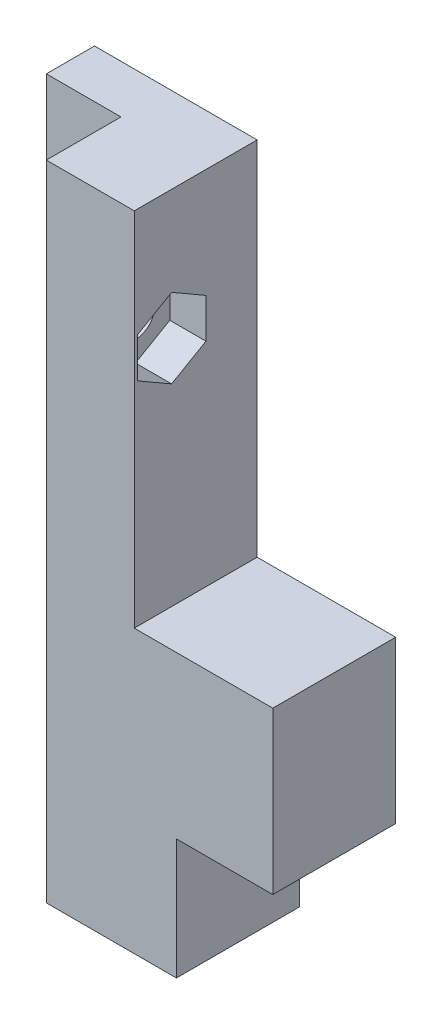
SolidWorks part; units mm, degrees
ref_plane "Alzado" through (0, 0, 0) normal (0, 0, 1) x (1, 0, 0)
ref_plane "Planta" through (0, 0, 0) normal (0, 1, 0) x (1, 0, 0)
ref_plane "Vista lateral" through (0, 0, 0) normal (1, 0, 0) x (0, 0, -1)
sketch "Croquis1" plane through (0, 0, 0) normal (0, 0, 1) x (1, 0, 0)
  line L1 (0, 0) -> (25, 0)
  line L2 (0, 0) -> (0, 35)
  line L3 (0, 35) -> (13.5, 35)
  line L4 (25, 0) -> (25, 5)
  line L7 (25, 5) -> (13.5, 5)
  line L8 (13.5, 35) -> (13.5, 5)
  dimension "D1" = 25
  dimension "D2" = 35
  dimension "D3" = 13.5
  dimension "D4" = 5
extrude "Saliente-Extruir1" add sketch "Croquis1" along normal blind 4
sketch "Croquis2" plane through (0, 0, 4) normal (0, 0, 1) x (1, 0, 0)
  line L0 (6.2, 35) -> (6.2, 0)
  line L1 (0, 35) -> (0, 0) construction
  line L6 (0, 35) -> (0, 0)
  line L7 (0, 0) -> (25, 0)
  line L8 (25, 0) -> (25, 5)
  line L9 (25, 5) -> (13.5, 5)
  line L10 (13.5, 5) -> (13.5, 35)
  line L11 (13.5, 35) -> (0, 35)
  line L13 (6.2, 0) -> (25, 0)
  line L14 (25, 0) -> (25, 5)
  line L15 (25, 5) -> (13.5, 5)
  line L16 (13.5, 5) -> (13.5, 35)
  line L17 (13.5, 35) -> (6.2, 35)
  dimension "D2" = 6.2
  dimension "D1" = 0
extrude "Saliente-Extruir2" add sketch "Croquis2" along normal blind 6.2
sketch "Croquis3" plane through (6.2, 0, 0) normal (-1, 0, 0) x (0, 0, 1)
  line L0 (7.1, 35) -> (7.1, 24.3) construction
  line L1 (10.2, 35) -> (4, 35) construction
  circle A0 centre (7.1, 24.3) radius 1.6
  dimension "D2" = 3.2
  dimension "D1" = 10.7
extrude "Cortar-Extruir1" cut sketch "Croquis3" against normal up to next
sketch "Croquis4" plane through (13.5, 0, 0) normal (1, 0, 0) x (0, 0, -1)
  line L1 (-7.1, 27.5909) -> (-9.95, 25.9454)
  line L2 (-9.95, 25.9454) -> (-9.95, 22.6546)
  line L3 (-9.95, 22.6546) -> (-7.1, 21.0091)
  line L4 (-7.1, 21.0091) -> (-4.25, 22.6546)
  line L5 (-4.25, 22.6546) -> (-4.25, 25.9454)
  line L6 (-4.25, 25.9454) -> (-7.1, 27.5909)
  circle A0 centre (-7.1, 24.3) radius 2.85 construction
  dimension "D1" = 5.7
extrude "Cortar-Extruir2" cut sketch "Croquis4" against normal blind 3
sketch "Croquis5" plane through (0, 0, 0) normal (0, -1, 0) x (1, 0, 0)
  line L6 (0, 0) -> (25, 0)
  line L7 (25, 0) -> (25, 10.2)
  line L8 (25, 10.2) -> (6.2, 10.2)
  line L9 (6.2, 10.2) -> (6.2, 4)
  line L10 (6.2, 4) -> (0, 4)
  line L11 (0, 4) -> (0, 0)
  line L12 (0, 0) -> (25, 0)
  line L13 (25, 0) -> (25, 10.2)
  line L14 (25, 10.2) -> (6.2, 10.2)
  line L15 (6.2, 10.2) -> (6.2, 4)
  line L16 (6.2, 4) -> (0, 4)
  line L17 (0, 4) -> (0, 0)
  dimension "D1" = 0
extrude "Saliente-Extruir3" add sketch "Croquis5" along normal blind 8.4
sketch "Croquis6" plane through (0, -8.4, 0) normal (0, -1, 0) x (1, 0, 0)
  line L0 (17, 0) -> (17, 10.2)
  line L6 (0, 4) -> (0, 0)
  line L7 (0, 0) -> (25, 0)
  line L8 (25, 0) -> (25, 10.2)
  line L9 (25, 10.2) -> (6.2, 10.2)
  line L10 (6.2, 10.2) -> (6.2, 4)
  line L11 (6.2, 4) -> (0, 4)
  line L12 (0, 4) -> (0, 0)
  line L13 (0, 0) -> (17, 0)
  line L15 (17, 10.2) -> (6.2, 10.2)
  line L16 (6.2, 10.2) -> (6.2, 4)
  line L17 (6.2, 4) -> (0, 4)
  dimension "D2" = 17
  dimension "D1" = 0
extrude "Saliente-Extruir4" add sketch "Croquis6" along normal blind 10
